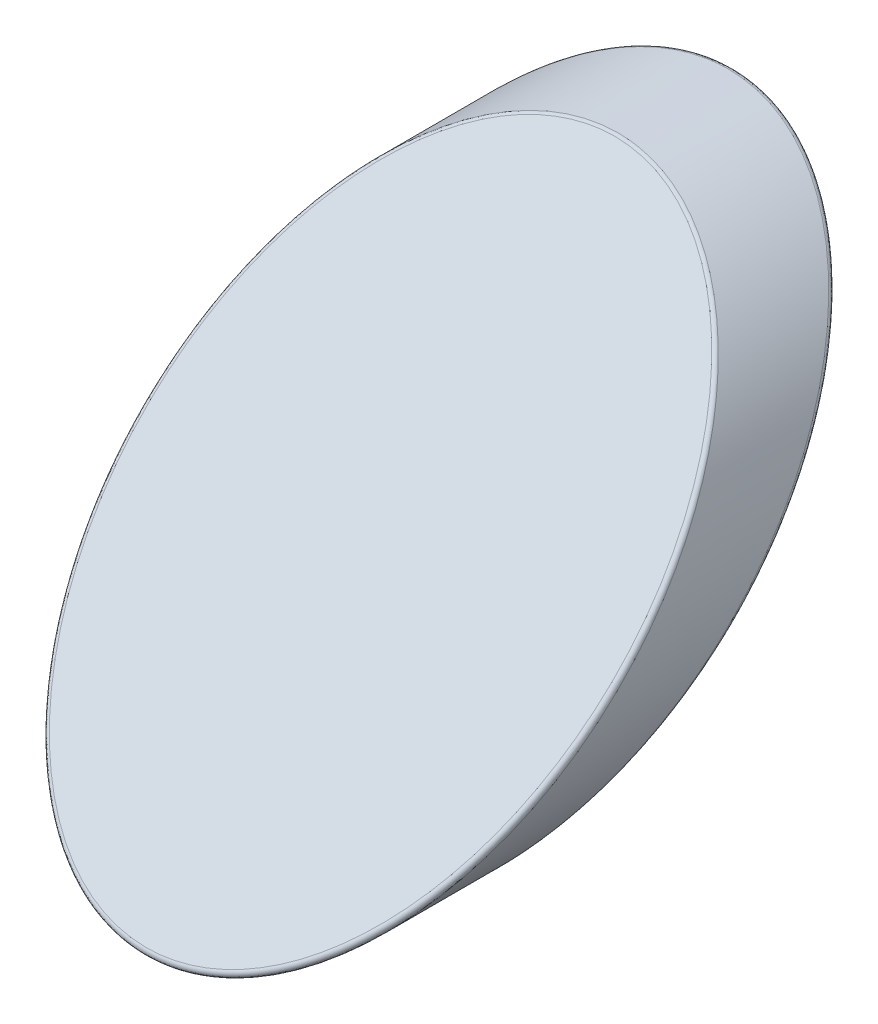
SolidWorks part; units mm, degrees
ref_plane "Top Plane" through (0, 0, 0) normal (0, 0, 1) x (1, 0, 0)
ref_plane "Front Plane" through (0, 0, 0) normal (0, 1, 0) x (1, 0, 0)
ref_plane "Right Plane" through (0, 0, 0) normal (1, 0, 0) x (0, 0, -1)
sketch "Sketch1" plane through (0, 0, 0) normal (0, 0, 1) x (1, 0, 0)
  circle A0 centre (0, 0) radius 26
  dimension "D1" = 52
extrude "Boss-Extrude1" add sketch "Sketch1" along normal blind 70
sketch "Sketch2" plane through (0, 0, 0) normal (1, 0, 0) x (0, 0, -1)
  line L0 (0, 26) -> (-52, -26)
  line L1 (-70, -26) -> (0, -26) construction
  line L2 (-65.435, -26) -> (-13.435, 26)
  line L3 (0, 26) -> (-70, 26) construction
  line L4 (-13.435, 26) -> (-70, 26)
  line L5 (-70, 26) -> (-70, -26)
  line L6 (-70, -26) -> (-65.435, -26)
  line L7 (-52, -26) -> (0, -26)
  line L8 (0, -26) -> (0, 26)
  dimension "D1" = 45
  dimension "D2" = 9.5
extrude "Cut-Extrude1" cut sketch "Sketch2" against normal through all both and the other way through all
fillet "Fillet1" radius 0.5 2 edges at (0, 26, 0) (0, 26, 13.435)
